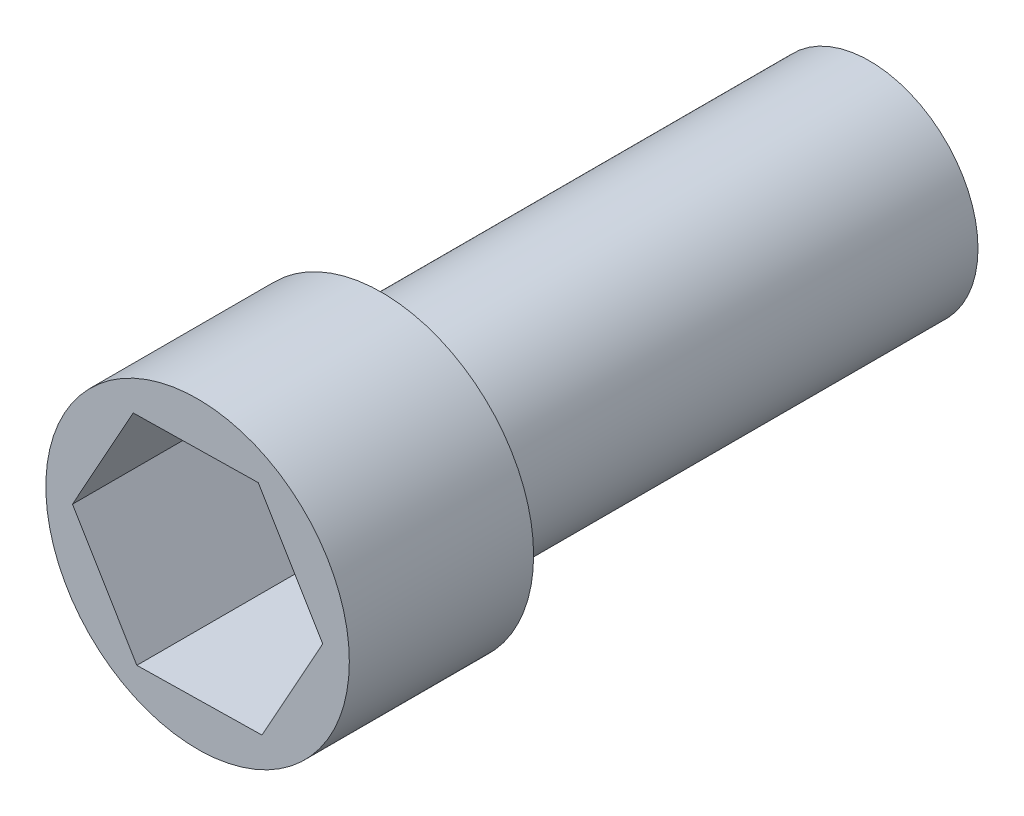
SolidWorks part; units mm, degrees
ref_plane "Front Plane" through (0, 0, 0) normal (0, 0, 1) x (1, 0, 0)
ref_plane "Top Plane" through (0, 0, 0) normal (0, 1, 0) x (1, 0, 0)
ref_plane "Right Plane" through (0, 0, 0) normal (1, 0, 0) x (0, 0, -1)
sketch "Sketch1" plane through (0, 0, 0) normal (0, 0, 1) x (1, 0, 0)
  circle A0 centre (0, 0) radius 14
  dimension "D1" = 28
extrude "Boss-Extrude1" add sketch "Sketch1" against normal blind 17
sketch "Sketch2" plane through (0, 0, -17) normal (0, 0, -1) x (-1, 0, 0)
  circle A0 centre (0, 0) radius 10
  dimension "D1" = 20
extrude "Boss-Extrude2" add sketch "Sketch2" along normal blind 45
sketch "Sketch3" plane through (0, 0, 0) normal (0, 0, 1) x (1, 0, 0)
  line L1 (5.6014, 10.0974) -> (-5.944, 9.8996)
  line L2 (-5.944, 9.8996) -> (-11.5453, -0.1978)
  line L3 (-11.5453, -0.1978) -> (-5.6014, -10.0974)
  line L4 (-5.6014, -10.0974) -> (5.944, -9.8996)
  line L5 (5.944, -9.8996) -> (11.5453, 0.1978)
  line L6 (11.5453, 0.1978) -> (5.6014, 10.0974)
  circle A0 centre (0, 0) radius 10 construction
  dimension "D1" = 20
extrude "Cut-Extrude1" cut sketch "Sketch3" against normal blind 16
